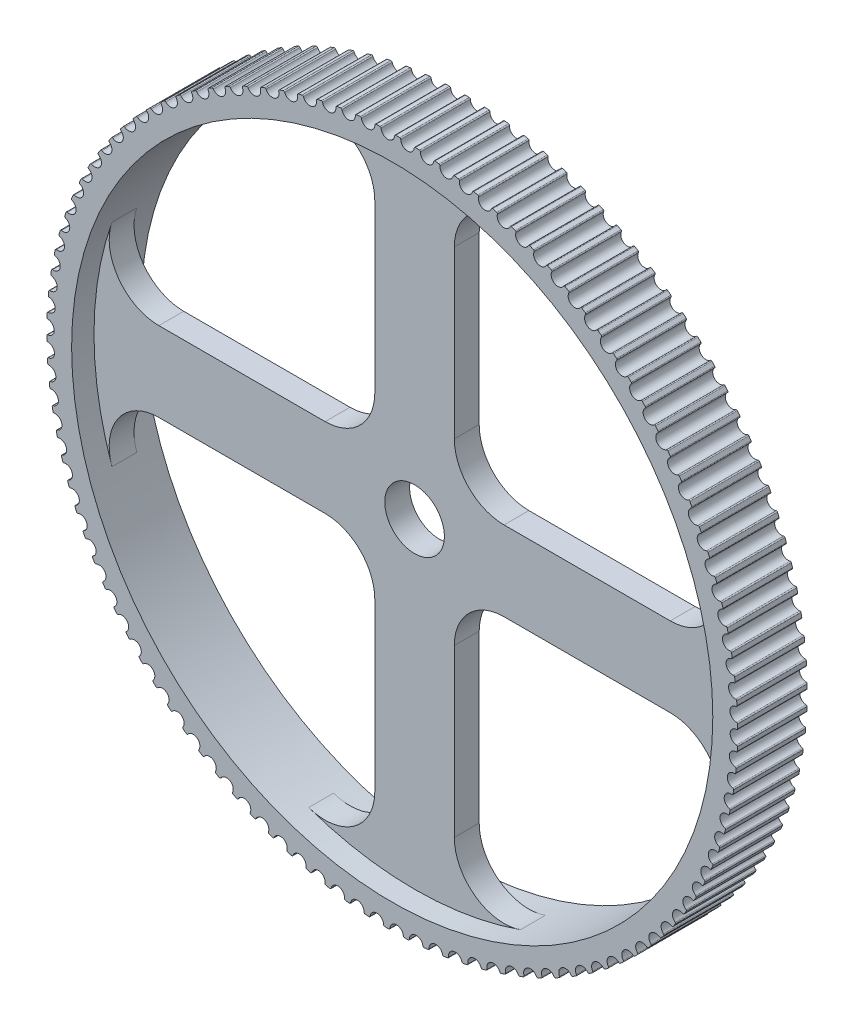
SolidWorks part; units mm, degrees
ref_plane "Front Plane" through (0, 0, 0) normal (0, 0, 1) x (1, 0, 0)
ref_plane "Top Plane" through (0, 0, 0) normal (0, 1, 0) x (1, 0, 0)
ref_plane "Right Plane" through (0, 0, 0) normal (1, 0, 0) x (0, 0, -1)
sketch "Sketch2" plane through (0, 0, 0) normal (0, 0, 1) x (1, 0, 0)
  circle A0 centre (0, 0) radius 35.03 construction
  arc A1 (-3.2113, 34.6013) -> (-3.0921, 34.5062) centre (-3.2012, 34.4918) cw
  arc A2 (-3.0921, 34.5062) -> (-1.738, 34.6009) centre (-2.418, 34.5956) ccw
  arc A3 (-1.738, 34.6009) -> (-1.6332, 34.7116) centre (-1.628, 34.6017) cw
  arc A4 (-1.6332, 34.7116) -> (-1.2307, 34.7282) centre (0, 0) cw
  circle A5 centre (0, 0) radius 34.75 construction
  circle A6 centre (0, 0) radius 34 construction
  arc A7 (0.3511, 34.7482) -> (0.7538, 34.7418) centre (0, 0) cw
  arc A8 (0.2401, 34.6437) -> (0.3511, 34.7482) centre (0.35, 34.6382) cw
  arc A9 (-1.1172, 34.6265) -> (0.2401, 34.6437) centre (-0.4391, 34.6772) ccw
  arc A10 (-1.2307, 34.7282) -> (-1.1172, 34.6265) centre (-1.2269, 34.6183) cw
  arc A11 (2.3343, 34.6715) -> (2.736, 34.6421) centre (0, 0) cw
  arc A12 (2.2175, 34.5735) -> (2.3343, 34.6715) centre (2.3269, 34.5618) cw
  arc A13 (0.8614, 34.6338) -> (2.2175, 34.5735) centre (1.5413, 34.6457) ccw
  arc A14 (0.7538, 34.7418) -> (0.8614, 34.6338) centre (0.7515, 34.6318) cw
  arc A15 (4.3098, 34.4817) -> (4.7092, 34.4294) centre (0, 0) cw
  arc A16 (4.1876, 34.3905) -> (4.3098, 34.4817) centre (4.2962, 34.3726) cw
  arc A17 (2.8372, 34.5281) -> (4.1876, 34.3905) centre (3.5167, 34.5012) ccw
  arc A18 (2.736, 34.6421) -> (2.8372, 34.5281) centre (2.7273, 34.5325) cw
  arc A19 (6.2713, 34.1794) -> (6.6671, 34.1044) centre (0, 0) cw
  arc A20 (6.1441, 34.0953) -> (6.2713, 34.1794) centre (6.2514, 34.0712) cw
  arc A21 (4.8038, 34.3098) -> (6.1441, 34.0953) centre (5.4806, 34.2442) ccw
  arc A22 (4.7092, 34.4294) -> (4.8038, 34.3098) centre (4.6943, 34.3204) cw
  arc A23 (8.2123, 33.7657) -> (8.6032, 33.6682) centre (0, 0) cw
  arc A24 (8.0806, 33.689) -> (8.2123, 33.7657) centre (8.1863, 33.6588) cw
  arc A25 (6.7547, 33.9796) -> (8.0806, 33.689) centre (7.4266, 33.8755) ccw
  arc A26 (6.6671, 34.1044) -> (6.7547, 33.9796) centre (6.646, 33.9965) cw
  arc A27 (10.1266, 33.2418) -> (10.5112, 33.1222) centre (0, 0) cw
  arc A28 (9.9906, 33.1727) -> (10.1266, 33.2418) centre (10.0945, 33.1365) cw
  arc A29 (8.6835, 33.5386) -> (9.9906, 33.1727) centre (9.3484, 33.3962) ccw
  arc A30 (8.6032, 33.6682) -> (8.6835, 33.5386) centre (8.5759, 33.5616) cw
  arc A31 (12.0078, 32.6094) -> (12.385, 32.4681) centre (0, 0) cw
  arc A32 (11.8681, 32.5482) -> (12.0078, 32.6094) centre (11.9698, 32.5062) cw
  arc A33 (10.584, 32.9882) -> (11.8681, 32.5482) centre (11.2397, 32.8081) ccw
  arc A34 (10.5112, 33.1222) -> (10.584, 32.9882) centre (10.4779, 33.0173) cw
  arc A35 (13.8498, 31.8707) -> (14.2183, 31.7081) centre (0, 0) cw
  arc A36 (13.7069, 31.8176) -> (13.8498, 31.8707) centre (13.806, 31.7699) cw
  arc A37 (12.45, 32.3301) -> (13.7069, 31.8176) centre (13.0944, 32.1129) ccw
  arc A38 (12.385, 32.4681) -> (12.45, 32.3301) centre (12.3458, 32.3653) cw
  arc A39 (15.6467, 31.0281) -> (16.0053, 30.8446) centre (0, 0) cw
  arc A40 (15.501, 30.9832) -> (15.6467, 31.0281) centre (15.5972, 30.9299) cw
  arc A41 (14.2754, 31.5667) -> (15.501, 30.9832) centre (14.9063, 31.313) ccw
  arc A42 (14.2183, 31.7081) -> (14.2754, 31.5667) centre (14.1733, 31.6077) cw
  arc A43 (17.3926, 30.0842) -> (17.7401, 29.8806) centre (0, 0) cw
  arc A44 (17.2445, 30.0478) -> (17.3926, 30.0842) centre (17.3375, 29.989) cw
  arc A45 (16.0542, 30.7002) -> (17.2445, 30.0478) centre (16.6696, 30.411) ccw
  arc A46 (16.0053, 30.8446) -> (16.0542, 30.7002) centre (15.9547, 30.747) cw
  arc A47 (19.0817, 29.0423) -> (19.417, 28.8191) centre (0, 0) cw
  arc A48 (18.9318, 29.0143) -> (19.0817, 29.0423) centre (19.0213, 28.9503) cw
  arc A49 (17.7807, 29.7336) -> (18.9318, 29.0143) centre (18.3786, 29.4097) ccw
  arc A50 (17.7401, 29.8806) -> (17.7807, 29.7336) centre (17.684, 29.786) cw
  arc A51 (20.7085, 27.9055) -> (21.0306, 27.6636) centre (0, 0) cw
  arc A52 (20.5573, 27.8862) -> (20.7085, 27.9055) centre (20.643, 27.8172) cw
  arc A53 (19.4491, 28.6701) -> (20.5573, 27.8862) centre (20.0276, 28.3125) ccw
  arc A54 (19.417, 28.8191) -> (19.4491, 28.6701) centre (19.3556, 28.7279) cw
  arc A55 (22.2679, 26.6778) -> (22.5756, 26.4179) centre (0, 0) cw
  arc A56 (22.1158, 26.6671) -> (22.2679, 26.6778) centre (22.1974, 26.5934) cw
  arc A57 (21.0542, 27.513) -> (22.1158, 26.6671) centre (21.6112, 27.123) ccw
  arc A58 (21.0306, 27.6636) -> (21.0542, 27.513) centre (20.964, 27.5761) cw
  arc A59 (23.7545, 25.363) -> (24.0469, 25.086) centre (0, 0) cw
  arc A60 (23.6021, 25.361) -> (23.7545, 25.363) centre (23.6793, 25.2828) cw
  arc A61 (22.5905, 26.2661) -> (23.6021, 25.361) centre (23.1244, 25.845) ccw
  arc A62 (22.5756, 26.4179) -> (22.5905, 26.2661) centre (22.5041, 26.3343) cw
  arc A63 (25.1637, 23.9656) -> (25.4399, 23.6723) centre (0, 0) cw
  arc A64 (25.0114, 23.9723) -> (25.1637, 23.9656) centre (25.0841, 23.8897) cw
  arc A65 (24.0532, 24.9336) -> (25.0114, 23.9723) centre (24.5621, 24.4827) ccw
  arc A66 (24.0469, 25.086) -> (24.0532, 24.9336) centre (23.9708, 25.0066) cw
  arc A67 (26.4909, 22.4899) -> (26.7498, 22.1813) centre (0, 0) cw
  arc A68 (26.3392, 22.5053) -> (26.4909, 22.4899) centre (26.407, 22.4187) cw
  arc A69 (25.4374, 23.5198) -> (26.3392, 22.5053) centre (25.9198, 23.0406) ccw
  arc A70 (25.4399, 23.6723) -> (25.4374, 23.5198) centre (25.3593, 23.5973) cw
  arc A71 (27.7316, 20.9409) -> (27.9725, 20.618) centre (0, 0) cw
  arc A72 (27.581, 20.9649) -> (27.7316, 20.9409) centre (27.6438, 20.8746) cw
  arc A73 (26.7386, 22.0293) -> (27.581, 20.9649) centre (27.1929, 21.5233) ccw
  arc A74 (26.7498, 22.1813) -> (26.7386, 22.0293) centre (26.6651, 22.1111) cw
  arc A75 (28.8819, 19.3236) -> (29.1039, 18.9875) centre (0, 0) cw
  arc A76 (28.7329, 19.3562) -> (28.8819, 19.3236) centre (28.7904, 19.2624) cw
  arc A77 (27.9526, 20.4669) -> (28.7329, 19.3562) centre (28.3772, 19.9358) ccw
  arc A78 (27.9725, 20.618) -> (27.9526, 20.4669) centre (27.8839, 20.5528) cw
  arc A79 (29.9379, 17.6432) -> (30.1404, 17.295) centre (0, 0) cw
  arc A80 (29.7911, 17.6843) -> (29.9379, 17.6432) centre (29.8431, 17.5874) cw
  arc A81 (29.0755, 18.8377) -> (29.7911, 17.6843) centre (29.4691, 18.2832) ccw
  arc A82 (29.1039, 18.9875) -> (29.0755, 18.8377) centre (29.0118, 18.9274) cw
  arc A83 (30.8963, 15.9053) -> (31.0786, 15.5461) centre (0, 0) cw
  arc A84 (30.752, 15.9547) -> (30.8963, 15.9053) centre (30.7985, 15.855) cw
  arc A85 (30.1035, 17.1471) -> (30.752, 15.9547) centre (30.4648, 16.571) ccw
  arc A86 (30.1404, 17.295) -> (30.1035, 17.1471) centre (30.045, 17.2403) cw
  arc A87 (31.7539, 14.1156) -> (31.9154, 13.7465) centre (0, 0) cw
  arc A88 (31.6127, 14.1731) -> (31.7539, 14.1156) centre (31.6534, 14.0709) cw
  arc A89 (31.0333, 15.4006) -> (31.6127, 14.1731) centre (31.3611, 14.8048) ccw
  arc A90 (31.0786, 15.5461) -> (31.0333, 15.4006) centre (30.9802, 15.4969) cw
  arc A91 (32.508, 12.2798) -> (32.6482, 11.9021) centre (0, 0) cw
  arc A92 (32.3703, 12.3452) -> (32.508, 12.2798) centre (32.4051, 12.2409) cw
  arc A93 (31.8619, 13.6038) -> (32.3703, 12.3452) centre (32.1552, 12.9903) ccw
  arc A94 (31.9154, 13.7465) -> (31.8619, 13.6038) centre (31.8144, 13.703) cw
  arc A95 (33.156, 10.4039) -> (33.2744, 10.0189) centre (0, 0) cw
  arc A96 (33.0223, 10.4771) -> (33.156, 10.4039) centre (33.0511, 10.371) cw
  arc A97 (32.5865, 11.7627) -> (33.0223, 10.4771) centre (32.8443, 11.1334) ccw
  arc A98 (32.6482, 11.9021) -> (32.5865, 11.7627) centre (32.5448, 11.8644) cw
  arc A99 (33.6959, 8.4941) -> (33.7921, 8.1029) centre (0, 0) cw
  arc A100 (33.5665, 8.5748) -> (33.6959, 8.4941) centre (33.5892, 8.4672) cw
  arc A101 (33.2049, 9.8831) -> (33.5665, 8.5748) centre (33.4263, 9.2402) ccw
  arc A102 (33.2744, 10.0189) -> (33.2049, 9.8831) centre (33.1691, 9.9871) cw
  arc A103 (34.1259, 6.5566) -> (34.1996, 6.1606) centre (0, 0) cw
  arc A104 (34.0013, 6.6446) -> (34.1259, 6.5566) centre (34.0178, 6.5358) cw
  arc A105 (33.7149, 7.9714) -> (34.0013, 6.6446) centre (33.8993, 7.3169) ccw
  arc A106 (33.7921, 8.1029) -> (33.7149, 7.9714) centre (33.6851, 8.0773) cw
  arc A107 (34.4445, 4.5977) -> (34.4955, 4.1981) centre (0, 0) cw
  arc A108 (34.3252, 4.6926) -> (34.4445, 4.5977) centre (34.3355, 4.5831) cw
  arc A109 (34.115, 6.0337) -> (34.3252, 4.6926) centre (34.2618, 5.3697) ccw
  arc A110 (34.1996, 6.1606) -> (34.115, 6.0337) centre (34.0913, 6.1411) cw
  arc A111 (34.6508, 2.6238) -> (34.6789, 2.2219) centre (0, 0) cw
  arc A112 (34.5371, 2.7254) -> (34.6508, 2.6238) centre (34.5411, 2.6155) cw
  arc A113 (34.4039, 4.0762) -> (34.5371, 2.7254) centre (34.5124, 3.4049) ccw
  arc A114 (34.4955, 4.1981) -> (34.4039, 4.0762) centre (34.3863, 4.1848) cw
  arc A115 (34.7441, 0.6413) -> (34.7492, 0.2385) centre (0, 0) cw
  arc A116 (34.6364, 0.7493) -> (34.7441, 0.6413) centre (34.6341, 0.6393) cw
  arc A117 (34.5805, 2.1055) -> (34.6364, 0.7493) centre (34.6505, 1.4291) ccw
  arc A118 (34.6789, 2.2219) -> (34.5805, 2.1055) centre (34.5691, 2.2149) cw
  arc A119 (34.724, -1.3432) -> (34.7061, -1.7456) centre (0, 0) cw
  arc A120 (34.6227, -1.2293) -> (34.724, -1.3432) centre (34.6141, -1.339) cw
  arc A121 (34.6443, 0.1279) -> (34.6227, -1.2293) centre (34.6756, -0.5514) ccw
  arc A122 (34.7492, 0.2385) -> (34.6443, 0.1279) centre (34.6392, 0.2378) cw
  arc A123 (34.5907, -3.3234) -> (34.5499, -3.7241) centre (0, 0) cw
  arc A124 (34.496, -3.2039) -> (34.5907, -3.3234) centre (34.4812, -3.3129) cw
  arc A125 (34.5951, -1.8501) -> (34.496, -3.2039) centre (34.5876, -2.5301) ccw
  arc A126 (34.7061, -1.7456) -> (34.5951, -1.8501) centre (34.5963, -1.7401) cw
  arc A127 (34.3446, -5.2927) -> (34.2809, -5.6905) centre (0, 0) cw
  arc A128 (34.2569, -5.168) -> (34.3446, -5.2927) centre (34.2359, -5.276) cw
  arc A129 (34.433, -3.8221) -> (34.2569, -5.168) centre (34.3867, -4.5005) ccw
  arc A130 (34.5499, -3.7241) -> (34.433, -3.8221) centre (34.4405, -3.7123) cw
  arc A131 (33.9864, -7.2448) -> (33.9001, -7.6382) centre (0, 0) cw
  arc A132 (33.906, -7.1152) -> (33.9864, -7.2448) centre (33.8788, -7.2218) cw
  arc A133 (34.1587, -5.7816) -> (33.906, -7.1152) centre (34.0737, -6.4563) ccw
  arc A134 (34.2809, -5.6905) -> (34.1587, -5.7816) centre (34.1724, -5.6724) cw
  arc A135 (33.5174, -9.1732) -> (33.4088, -9.5611) centre (0, 0) cw
  arc A136 (33.4445, -9.0393) -> (33.5174, -9.1732) centre (33.4113, -9.1442) cw
  arc A137 (33.7729, -7.7222) -> (33.4445, -9.0393) centre (33.6496, -8.391) ccw
  arc A138 (33.9001, -7.6382) -> (33.7729, -7.7222) centre (33.7928, -7.6141) cw
  arc A139 (32.939, -11.0717) -> (32.8085, -11.4528) centre (0, 0) cw
  arc A140 (32.8739, -10.9338) -> (32.939, -11.0717) centre (32.8348, -11.0367) cw
  arc A141 (33.277, -9.6377) -> (32.8739, -10.9338) centre (33.1157, -10.2983) ccw
  arc A142 (33.4088, -9.5611) -> (33.277, -9.6377) centre (33.303, -9.5308) cw
  arc A143 (32.2532, -12.9341) -> (32.1012, -13.3071) centre (0, 0) cw
  arc A144 (32.1961, -12.7927) -> (32.2532, -12.9341) centre (32.1511, -12.8932) cw
  arc A145 (32.6725, -11.5217) -> (32.1961, -12.7927) centre (32.4737, -12.172) ccw
  arc A146 (32.8085, -11.4528) -> (32.6725, -11.5217) centre (32.7046, -11.4165) cw
  arc A147 (31.4622, -14.7543) -> (31.2891, -15.118) centre (0, 0) cw
  arc A148 (31.4132, -14.6099) -> (31.4622, -14.7543) centre (31.3627, -14.7076) cw
  arc A149 (31.9614, -13.3682) -> (31.4132, -14.6099) centre (31.7259, -14.0061) ccw
  arc A150 (32.1012, -13.3071) -> (31.9614, -13.3682) centre (31.9995, -13.265) cw
  arc A151 (30.5686, -16.5264) -> (30.375, -16.8796) centre (0, 0) cw
  arc A152 (30.5279, -16.3794) -> (30.5686, -16.5264) centre (30.4719, -16.4741) cw
  arc A153 (31.1461, -15.171) -> (30.5279, -16.3794) centre (30.8746, -15.7944) ccw
  arc A154 (31.2891, -15.118) -> (31.1461, -15.171) centre (31.1901, -15.0701) cw
  arc A155 (29.5753, -18.2446) -> (29.3618, -18.5861) centre (0, 0) cw
  arc A156 (29.5431, -18.0955) -> (29.5753, -18.2446) centre (29.4817, -18.1868) cw
  arc A157 (30.2292, -16.9243) -> (29.5431, -18.0955) centre (29.9225, -17.5312) ccw
  arc A158 (30.375, -16.8796) -> (30.2292, -16.9243) centre (30.2789, -16.8262) cw
  arc A159 (28.4855, -19.9032) -> (28.2529, -20.2321) centre (0, 0) cw
  arc A160 (28.4618, -19.7526) -> (28.4855, -19.9032) centre (28.3953, -19.8402) cw
  arc A161 (29.2138, -18.6225) -> (28.4618, -19.7526) centre (28.8729, -19.2109) ccw
  arc A162 (29.3618, -18.5861) -> (29.2138, -18.6225) centre (29.2689, -18.5273) cw
  arc A163 (27.3028, -21.497) -> (27.0518, -21.812) centre (0, 0) cw
  arc A164 (27.2878, -21.3452) -> (27.3028, -21.497) centre (27.2164, -21.4289) cw
  arc A165 (28.103, -20.2599) -> (27.2878, -21.3452) centre (27.7291, -20.8279) ccw
  arc A166 (28.2529, -20.2321) -> (28.103, -20.2599) centre (28.1635, -20.168) cw
  arc A167 (26.031, -23.0206) -> (25.7625, -23.3208) centre (0, 0) cw
  arc A168 (26.0247, -22.8682) -> (26.031, -23.0206) centre (25.9486, -22.9477) cw
  arc A169 (26.9005, -21.8312) -> (26.0247, -22.8682) centre (26.4948, -22.3769) ccw
  arc A170 (27.0518, -21.812) -> (26.9005, -21.8312) centre (26.9662, -21.743) cw
  arc A171 (24.6744, -24.4691) -> (24.3891, -24.7535) centre (0, 0) cw
  arc A172 (24.6767, -24.3167) -> (24.6744, -24.4691) centre (24.5963, -24.3917) cw
  arc A173 (25.6103, -23.3313) -> (24.6767, -24.3167) centre (25.1741, -23.853) ccw
  arc A174 (25.7625, -23.3208) -> (25.6103, -23.3313) centre (25.6809, -23.247) cw
  arc A175 (23.2372, -25.8378) -> (22.9362, -26.1055) centre (0, 0) cw
  arc A176 (23.2483, -25.6858) -> (23.2372, -25.8378) centre (23.1637, -25.7561) cw
  arc A177 (24.2366, -24.7554) -> (23.2483, -25.6858) centre (23.7713, -25.2513) ccw
  arc A178 (24.3891, -24.7535) -> (24.2366, -24.7554) centre (24.3119, -24.6751) cw
  arc A179 (21.7243, -27.1223) -> (21.4084, -27.3723) centre (0, 0) cw
  arc A180 (21.744, -26.9711) -> (21.7243, -27.1223) centre (21.6555, -27.0364) cw
  arc A181 (22.7838, -26.0986) -> (21.744, -26.9711) centre (22.291, -26.5672) ccw
  arc A182 (22.9362, -26.1055) -> (22.7838, -26.0986) centre (22.8636, -26.0228) cw
  arc A183 (20.1405, -28.3183) -> (19.8109, -28.5498) centre (0, 0) cw
  arc A184 (20.1688, -28.1684) -> (20.1405, -28.3183) centre (20.0767, -28.2286) cw
  arc A185 (21.2567, -27.3568) -> (20.1688, -28.1684) centre (20.738, -27.7964) ccw
  arc A186 (21.4084, -27.3723) -> (21.2567, -27.3568) centre (21.3407, -27.2856) cw
  arc A187 (18.491, -29.4219) -> (18.1487, -29.6342) centre (0, 0) cw
  arc A188 (18.5278, -29.2739) -> (18.491, -29.4219) centre (18.4324, -29.3287) cw
  arc A189 (19.6603, -28.5257) -> (18.5278, -29.2739) centre (19.1173, -28.935) ccw
  arc A190 (19.8109, -28.5498) -> (19.6603, -28.5257) centre (19.7481, -28.4595) cw
  arc A191 (16.7811, -30.4295) -> (16.4273, -30.622) centre (0, 0) cw
  arc A192 (16.8263, -30.2839) -> (16.7811, -30.4295) centre (16.728, -30.3332) cw
  arc A193 (17.9997, -29.6015) -> (16.8263, -30.2839) centre (17.4342, -29.9792) ccw
  arc A194 (18.1487, -29.6342) -> (17.9997, -29.6015) centre (18.0912, -29.5404) cw
  arc A195 (15.0166, -31.3379) -> (14.6523, -31.5099) centre (0, 0) cw
  arc A196 (15.07, -31.1951) -> (15.0166, -31.3379) centre (14.969, -31.2387) cw
  arc A197 (16.2805, -30.5808) -> (15.07, -31.1951) centre (15.6943, -30.9256) ccw
  arc A198 (16.4273, -30.622) -> (16.2805, -30.5808) centre (16.3753, -30.5251) cw
  arc A199 (13.203, -32.1441) -> (12.8296, -32.295) centre (0, 0) cw
  arc A200 (13.2646, -32.0046) -> (13.203, -32.1441) centre (13.1613, -32.0423) cw
  arc A201 (14.5081, -31.4604) -> (13.2646, -32.0046) centre (13.9032, -31.7711) ccw
  arc A202 (14.6523, -31.5099) -> (14.5081, -31.4604) centre (14.6059, -31.4101) cw
  arc A203 (11.3464, -32.8454) -> (10.965, -32.9747) centre (0, 0) cw
  arc A204 (11.4158, -32.7096) -> (11.3464, -32.8454) centre (11.3105, -32.7414) cw
  arc A205 (12.6884, -32.2373) -> (11.4158, -32.7096) centre (12.0668, -32.513) ccw
  arc A206 (12.8296, -32.295) -> (12.6884, -32.2373) centre (12.789, -32.1927) cw
  arc A207 (9.4528, -33.4396) -> (9.0646, -33.5469) centre (0, 0) cw
  arc A208 (9.5299, -33.308) -> (9.4528, -33.4396) centre (9.4229, -33.3337) cw
  arc A209 (10.8273, -32.9091) -> (9.5299, -33.308) centre (10.191, -33.1489) ccw
  arc A210 (10.965, -32.9747) -> (10.8273, -32.9091) centre (10.9302, -32.8703) cw
  arc A211 (7.5284, -33.9247) -> (7.1347, -34.0097) centre (0, 0) cw
  arc A212 (7.6128, -33.7977) -> (7.5284, -33.9247) centre (7.5046, -33.8173) cw
  arc A213 (8.9309, -33.4736) -> (7.6128, -33.7977) centre (8.2819, -33.6766) ccw
  arc A214 (9.0646, -33.5469) -> (8.9309, -33.4736) centre (9.0359, -33.4407) cw
  arc A215 (5.5794, -34.2992) -> (5.1814, -34.3615) centre (0, 0) cw
  arc A216 (5.6709, -34.1772) -> (5.5794, -34.2992) centre (5.5617, -34.1906) cw
  arc A217 (7.0054, -33.9288) -> (5.6709, -34.1772) centre (6.3459, -34.0945) ccw
  arc A218 (7.1347, -34.0097) -> (7.0054, -33.9288) centre (7.1121, -33.902) cw
  arc A219 (3.6122, -34.5617) -> (3.2113, -34.6013) centre (0, 0) cw
  arc A220 (3.7105, -34.4452) -> (3.6122, -34.5617) centre (3.6008, -34.4523) cw
  arc A221 (5.057, -34.2734) -> (3.7105, -34.4452) centre (4.3891, -34.4011) ccw
  arc A222 (5.1814, -34.3615) -> (5.057, -34.2734) centre (5.165, -34.2528) cw
  arc A223 (1.6332, -34.7116) -> (1.2307, -34.7282) centre (0, 0) cw
  arc A224 (1.738, -34.6009) -> (1.6332, -34.7116) centre (1.628, -34.6017) cw
  arc A225 (3.0921, -34.5062) -> (1.738, -34.6009) centre (2.418, -34.5956) ccw
  arc A226 (3.2113, -34.6013) -> (3.0921, -34.5062) centre (3.2012, -34.4918) cw
  arc A227 (-0.3511, -34.7482) -> (-0.7538, -34.7418) centre (0, 0) cw
  arc A228 (-0.2401, -34.6437) -> (-0.3511, -34.7482) centre (-0.35, -34.6382) cw
  arc A229 (1.1172, -34.6265) -> (-0.2401, -34.6437) centre (0.4391, -34.6772) ccw
  arc A230 (1.2307, -34.7282) -> (1.1172, -34.6265) centre (1.2269, -34.6183) cw
  arc A231 (-2.3343, -34.6715) -> (-2.736, -34.6421) centre (0, 0) cw
  arc A232 (-2.2175, -34.5735) -> (-2.3343, -34.6715) centre (-2.3269, -34.5618) cw
  arc A233 (-0.8614, -34.6338) -> (-2.2175, -34.5735) centre (-1.5413, -34.6457) ccw
  arc A234 (-0.7538, -34.7418) -> (-0.8614, -34.6338) centre (-0.7515, -34.6318) cw
  arc A235 (-4.3098, -34.4817) -> (-4.7092, -34.4294) centre (0, 0) cw
  arc A236 (-4.1876, -34.3905) -> (-4.3098, -34.4817) centre (-4.2962, -34.3726) cw
  arc A237 (-2.8372, -34.5281) -> (-4.1876, -34.3905) centre (-3.5167, -34.5012) ccw
  arc A238 (-2.736, -34.6421) -> (-2.8372, -34.5281) centre (-2.7273, -34.5325) cw
  arc A239 (-6.2713, -34.1794) -> (-6.6671, -34.1044) centre (0, 0) cw
  arc A240 (-6.1441, -34.0953) -> (-6.2713, -34.1794) centre (-6.2514, -34.0712) cw
  arc A241 (-4.8038, -34.3098) -> (-6.1441, -34.0953) centre (-5.4806, -34.2442) ccw
  arc A242 (-4.7092, -34.4294) -> (-4.8038, -34.3098) centre (-4.6943, -34.3204) cw
  arc A243 (-8.2123, -33.7657) -> (-8.6032, -33.6682) centre (0, 0) cw
  arc A244 (-8.0806, -33.689) -> (-8.2123, -33.7657) centre (-8.1863, -33.6588) cw
  arc A245 (-6.7547, -33.9796) -> (-8.0806, -33.689) centre (-7.4266, -33.8755) ccw
  arc A246 (-6.6671, -34.1044) -> (-6.7547, -33.9796) centre (-6.646, -33.9965) cw
  arc A247 (-10.1266, -33.2418) -> (-10.5112, -33.1222) centre (0, 0) cw
  arc A248 (-9.9906, -33.1727) -> (-10.1266, -33.2418) centre (-10.0945, -33.1365) cw
  arc A249 (-8.6835, -33.5386) -> (-9.9906, -33.1727) centre (-9.3484, -33.3962) ccw
  arc A250 (-8.6032, -33.6682) -> (-8.6835, -33.5386) centre (-8.5759, -33.5616) cw
  arc A251 (-12.0078, -32.6094) -> (-12.385, -32.4681) centre (0, 0) cw
  arc A252 (-11.8681, -32.5482) -> (-12.0078, -32.6094) centre (-11.9698, -32.5062) cw
  arc A253 (-10.584, -32.9882) -> (-11.8681, -32.5482) centre (-11.2397, -32.8081) ccw
  arc A254 (-10.5112, -33.1222) -> (-10.584, -32.9882) centre (-10.4779, -33.0173) cw
  arc A255 (-13.8498, -31.8707) -> (-14.2183, -31.7081) centre (0, 0) cw
  arc A256 (-13.7069, -31.8176) -> (-13.8498, -31.8707) centre (-13.806, -31.7699) cw
  arc A257 (-12.45, -32.3301) -> (-13.7069, -31.8176) centre (-13.0944, -32.1129) ccw
  arc A258 (-12.385, -32.4681) -> (-12.45, -32.3301) centre (-12.3458, -32.3653) cw
  arc A259 (-15.6467, -31.0281) -> (-16.0053, -30.8446) centre (0, 0) cw
  arc A260 (-15.501, -30.9832) -> (-15.6467, -31.0281) centre (-15.5972, -30.9299) cw
  arc A261 (-14.2754, -31.5667) -> (-15.501, -30.9832) centre (-14.9063, -31.313) ccw
  arc A262 (-14.2183, -31.7081) -> (-14.2754, -31.5667) centre (-14.1733, -31.6077) cw
  arc A263 (-17.3926, -30.0842) -> (-17.7401, -29.8806) centre (0, 0) cw
  arc A264 (-17.2445, -30.0478) -> (-17.3926, -30.0842) centre (-17.3375, -29.989) cw
  arc A265 (-16.0542, -30.7002) -> (-17.2445, -30.0478) centre (-16.6696, -30.411) ccw
  arc A266 (-16.0053, -30.8446) -> (-16.0542, -30.7002) centre (-15.9547, -30.747) cw
  arc A267 (-19.0817, -29.0423) -> (-19.417, -28.8191) centre (0, 0) cw
  arc A268 (-18.9318, -29.0143) -> (-19.0817, -29.0423) centre (-19.0213, -28.9503) cw
  arc A269 (-17.7807, -29.7336) -> (-18.9318, -29.0143) centre (-18.3786, -29.4097) ccw
  arc A270 (-17.7401, -29.8806) -> (-17.7807, -29.7336) centre (-17.684, -29.786) cw
  arc A271 (-20.7085, -27.9055) -> (-21.0306, -27.6636) centre (0, 0) cw
  arc A272 (-20.5573, -27.8862) -> (-20.7085, -27.9055) centre (-20.643, -27.8172) cw
  arc A273 (-19.4491, -28.6701) -> (-20.5573, -27.8862) centre (-20.0276, -28.3125) ccw
  arc A274 (-19.417, -28.8191) -> (-19.4491, -28.6701) centre (-19.3556, -28.7279) cw
  arc A275 (-22.2679, -26.6778) -> (-22.5756, -26.4179) centre (0, 0) cw
  arc A276 (-22.1158, -26.6671) -> (-22.2679, -26.6778) centre (-22.1974, -26.5934) cw
  arc A277 (-21.0542, -27.513) -> (-22.1158, -26.6671) centre (-21.6112, -27.123) ccw
  arc A278 (-21.0306, -27.6636) -> (-21.0542, -27.513) centre (-20.964, -27.5761) cw
  arc A279 (-23.7545, -25.363) -> (-24.0469, -25.086) centre (0, 0) cw
  arc A280 (-23.6021, -25.361) -> (-23.7545, -25.363) centre (-23.6793, -25.2828) cw
  arc A281 (-22.5905, -26.2661) -> (-23.6021, -25.361) centre (-23.1244, -25.845) ccw
  arc A282 (-22.5756, -26.4179) -> (-22.5905, -26.2661) centre (-22.5041, -26.3343) cw
  arc A283 (-25.1637, -23.9656) -> (-25.4399, -23.6723) centre (0, 0) cw
  arc A284 (-25.0114, -23.9723) -> (-25.1637, -23.9656) centre (-25.0841, -23.8897) cw
  arc A285 (-24.0532, -24.9336) -> (-25.0114, -23.9723) centre (-24.5621, -24.4827) ccw
  arc A286 (-24.0469, -25.086) -> (-24.0532, -24.9336) centre (-23.9708, -25.0066) cw
  arc A287 (-26.4909, -22.4899) -> (-26.7498, -22.1813) centre (0, 0) cw
  arc A288 (-26.3392, -22.5053) -> (-26.4909, -22.4899) centre (-26.407, -22.4187) cw
  arc A289 (-25.4374, -23.5198) -> (-26.3392, -22.5053) centre (-25.9198, -23.0406) ccw
  arc A290 (-25.4399, -23.6723) -> (-25.4374, -23.5198) centre (-25.3593, -23.5973) cw
  arc A291 (-27.7316, -20.9409) -> (-27.9725, -20.618) centre (0, 0) cw
  arc A292 (-27.581, -20.9649) -> (-27.7316, -20.9409) centre (-27.6438, -20.8746) cw
  arc A293 (-26.7386, -22.0293) -> (-27.581, -20.9649) centre (-27.1929, -21.5233) ccw
  arc A294 (-26.7498, -22.1813) -> (-26.7386, -22.0293) centre (-26.6651, -22.1111) cw
  arc A295 (-28.8819, -19.3236) -> (-29.1039, -18.9875) centre (0, 0) cw
  arc A296 (-28.7329, -19.3562) -> (-28.8819, -19.3236) centre (-28.7904, -19.2624) cw
  arc A297 (-27.9526, -20.4669) -> (-28.7329, -19.3562) centre (-28.3772, -19.9358) ccw
  arc A298 (-27.9725, -20.618) -> (-27.9526, -20.4669) centre (-27.8839, -20.5528) cw
  arc A299 (-29.9379, -17.6432) -> (-30.1404, -17.295) centre (0, 0) cw
  arc A300 (-29.7911, -17.6843) -> (-29.9379, -17.6432) centre (-29.8431, -17.5874) cw
  arc A301 (-29.0755, -18.8377) -> (-29.7911, -17.6843) centre (-29.4691, -18.2832) ccw
  arc A302 (-29.1039, -18.9875) -> (-29.0755, -18.8377) centre (-29.0118, -18.9274) cw
  arc A303 (-30.8963, -15.9053) -> (-31.0786, -15.5461) centre (0, 0) cw
  arc A304 (-30.752, -15.9547) -> (-30.8963, -15.9053) centre (-30.7985, -15.855) cw
  arc A305 (-30.1035, -17.1471) -> (-30.752, -15.9547) centre (-30.4648, -16.571) ccw
  arc A306 (-30.1404, -17.295) -> (-30.1035, -17.1471) centre (-30.045, -17.2403) cw
  arc A307 (-31.7539, -14.1156) -> (-31.9154, -13.7465) centre (0, 0) cw
  arc A308 (-31.6127, -14.1731) -> (-31.7539, -14.1156) centre (-31.6534, -14.0709) cw
  arc A309 (-31.0333, -15.4006) -> (-31.6127, -14.1731) centre (-31.3611, -14.8048) ccw
  arc A310 (-31.0786, -15.5461) -> (-31.0333, -15.4006) centre (-30.9802, -15.4969) cw
  arc A311 (-32.508, -12.2798) -> (-32.6482, -11.9021) centre (0, 0) cw
  arc A312 (-32.3703, -12.3452) -> (-32.508, -12.2798) centre (-32.4051, -12.2409) cw
  arc A313 (-31.8619, -13.6038) -> (-32.3703, -12.3452) centre (-32.1552, -12.9903) ccw
  arc A314 (-31.9154, -13.7465) -> (-31.8619, -13.6038) centre (-31.8144, -13.703) cw
  arc A315 (-33.156, -10.4039) -> (-33.2744, -10.0189) centre (0, 0) cw
  arc A316 (-33.0223, -10.4771) -> (-33.156, -10.4039) centre (-33.0511, -10.371) cw
  arc A317 (-32.5865, -11.7627) -> (-33.0223, -10.4771) centre (-32.8443, -11.1334) ccw
  arc A318 (-32.6482, -11.9021) -> (-32.5865, -11.7627) centre (-32.5448, -11.8644) cw
  arc A319 (-33.6959, -8.4941) -> (-33.7921, -8.1029) centre (0, 0) cw
  arc A320 (-33.5665, -8.5748) -> (-33.6959, -8.4941) centre (-33.5892, -8.4672) cw
  arc A321 (-33.2049, -9.8831) -> (-33.5665, -8.5748) centre (-33.4263, -9.2402) ccw
  arc A322 (-33.2744, -10.0189) -> (-33.2049, -9.8831) centre (-33.1691, -9.9871) cw
  arc A323 (-34.1259, -6.5566) -> (-34.1996, -6.1606) centre (0, 0) cw
  arc A324 (-34.0013, -6.6446) -> (-34.1259, -6.5566) centre (-34.0178, -6.5358) cw
  arc A325 (-33.7149, -7.9714) -> (-34.0013, -6.6446) centre (-33.8993, -7.3169) ccw
  arc A326 (-33.7921, -8.1029) -> (-33.7149, -7.9714) centre (-33.6851, -8.0773) cw
  arc A327 (-34.4445, -4.5977) -> (-34.4955, -4.1981) centre (0, 0) cw
  arc A328 (-34.3252, -4.6926) -> (-34.4445, -4.5977) centre (-34.3355, -4.5831) cw
  arc A329 (-34.115, -6.0337) -> (-34.3252, -4.6926) centre (-34.2618, -5.3697) ccw
  arc A330 (-34.1996, -6.1606) -> (-34.115, -6.0337) centre (-34.0913, -6.1411) cw
  arc A331 (-34.6508, -2.6238) -> (-34.6789, -2.2219) centre (0, 0) cw
  arc A332 (-34.5371, -2.7254) -> (-34.6508, -2.6238) centre (-34.5411, -2.6155) cw
  arc A333 (-34.4039, -4.0762) -> (-34.5371, -2.7254) centre (-34.5124, -3.4049) ccw
  arc A334 (-34.4955, -4.1981) -> (-34.4039, -4.0762) centre (-34.3863, -4.1848) cw
  arc A335 (-34.7441, -0.6413) -> (-34.7492, -0.2385) centre (0, 0) cw
  arc A336 (-34.6364, -0.7493) -> (-34.7441, -0.6413) centre (-34.6341, -0.6393) cw
  arc A337 (-34.5805, -2.1055) -> (-34.6364, -0.7493) centre (-34.6505, -1.4291) ccw
  arc A338 (-34.6789, -2.2219) -> (-34.5805, -2.1055) centre (-34.5691, -2.2149) cw
  arc A339 (-34.724, 1.3432) -> (-34.7061, 1.7456) centre (0, 0) cw
  arc A340 (-34.6227, 1.2293) -> (-34.724, 1.3432) centre (-34.6141, 1.339) cw
  arc A341 (-34.6443, -0.1279) -> (-34.6227, 1.2293) centre (-34.6756, 0.5514) ccw
  arc A342 (-34.7492, -0.2385) -> (-34.6443, -0.1279) centre (-34.6392, -0.2378) cw
  arc A343 (-34.5907, 3.3234) -> (-34.5499, 3.7241) centre (0, 0) cw
  arc A344 (-34.496, 3.2039) -> (-34.5907, 3.3234) centre (-34.4812, 3.3129) cw
  arc A345 (-34.5951, 1.8501) -> (-34.496, 3.2039) centre (-34.5876, 2.5301) ccw
  arc A346 (-34.7061, 1.7456) -> (-34.5951, 1.8501) centre (-34.5963, 1.7401) cw
  arc A347 (-34.3446, 5.2927) -> (-34.2809, 5.6905) centre (0, 0) cw
  arc A348 (-34.2569, 5.168) -> (-34.3446, 5.2927) centre (-34.2359, 5.276) cw
  arc A349 (-34.433, 3.8221) -> (-34.2569, 5.168) centre (-34.3867, 4.5005) ccw
  arc A350 (-34.5499, 3.7241) -> (-34.433, 3.8221) centre (-34.4405, 3.7123) cw
  arc A351 (-33.9864, 7.2448) -> (-33.9001, 7.6382) centre (0, 0) cw
  arc A352 (-33.906, 7.1152) -> (-33.9864, 7.2448) centre (-33.8788, 7.2218) cw
  arc A353 (-34.1587, 5.7816) -> (-33.906, 7.1152) centre (-34.0737, 6.4563) ccw
  arc A354 (-34.2809, 5.6905) -> (-34.1587, 5.7816) centre (-34.1724, 5.6724) cw
  arc A355 (-33.5174, 9.1732) -> (-33.4088, 9.5611) centre (0, 0) cw
  arc A356 (-33.4445, 9.0393) -> (-33.5174, 9.1732) centre (-33.4113, 9.1442) cw
  arc A357 (-33.7729, 7.7222) -> (-33.4445, 9.0393) centre (-33.6496, 8.391) ccw
  arc A358 (-33.9001, 7.6382) -> (-33.7729, 7.7222) centre (-33.7928, 7.6141) cw
  arc A359 (-32.939, 11.0717) -> (-32.8085, 11.4528) centre (0, 0) cw
  arc A360 (-32.8739, 10.9338) -> (-32.939, 11.0717) centre (-32.8348, 11.0367) cw
  arc A361 (-33.277, 9.6377) -> (-32.8739, 10.9338) centre (-33.1157, 10.2983) ccw
  arc A362 (-33.4088, 9.5611) -> (-33.277, 9.6377) centre (-33.303, 9.5308) cw
  arc A363 (-32.2532, 12.9341) -> (-32.1012, 13.3071) centre (0, 0) cw
  arc A364 (-32.1961, 12.7927) -> (-32.2532, 12.9341) centre (-32.1511, 12.8932) cw
  arc A365 (-32.6725, 11.5217) -> (-32.1961, 12.7927) centre (-32.4737, 12.172) ccw
  arc A366 (-32.8085, 11.4528) -> (-32.6725, 11.5217) centre (-32.7046, 11.4165) cw
  arc A367 (-31.4622, 14.7543) -> (-31.2891, 15.118) centre (0, 0) cw
  arc A368 (-31.4132, 14.6099) -> (-31.4622, 14.7543) centre (-31.3627, 14.7076) cw
  arc A369 (-31.9614, 13.3682) -> (-31.4132, 14.6099) centre (-31.7259, 14.0061) ccw
  arc A370 (-32.1012, 13.3071) -> (-31.9614, 13.3682) centre (-31.9995, 13.265) cw
  arc A371 (-30.5686, 16.5264) -> (-30.375, 16.8796) centre (0, 0) cw
  arc A372 (-30.5279, 16.3794) -> (-30.5686, 16.5264) centre (-30.4719, 16.4741) cw
  arc A373 (-31.1461, 15.171) -> (-30.5279, 16.3794) centre (-30.8746, 15.7944) ccw
  arc A374 (-31.2891, 15.118) -> (-31.1461, 15.171) centre (-31.1901, 15.0701) cw
  arc A375 (-29.5753, 18.2446) -> (-29.3618, 18.5861) centre (0, 0) cw
  arc A376 (-29.5431, 18.0955) -> (-29.5753, 18.2446) centre (-29.4817, 18.1868) cw
  arc A377 (-30.2292, 16.9243) -> (-29.5431, 18.0955) centre (-29.9225, 17.5312) ccw
  arc A378 (-30.375, 16.8796) -> (-30.2292, 16.9243) centre (-30.2789, 16.8262) cw
  arc A379 (-28.4855, 19.9032) -> (-28.2529, 20.2321) centre (0, 0) cw
  arc A380 (-28.4618, 19.7526) -> (-28.4855, 19.9032) centre (-28.3953, 19.8402) cw
  arc A381 (-29.2138, 18.6225) -> (-28.4618, 19.7526) centre (-28.8729, 19.2109) ccw
  arc A382 (-29.3618, 18.5861) -> (-29.2138, 18.6225) centre (-29.2689, 18.5273) cw
  arc A383 (-27.3028, 21.497) -> (-27.0518, 21.812) centre (0, 0) cw
  arc A384 (-27.2878, 21.3452) -> (-27.3028, 21.497) centre (-27.2164, 21.4289) cw
  arc A385 (-28.103, 20.2599) -> (-27.2878, 21.3452) centre (-27.7291, 20.8279) ccw
  arc A386 (-28.2529, 20.2321) -> (-28.103, 20.2599) centre (-28.1635, 20.168) cw
  arc A387 (-26.031, 23.0206) -> (-25.7625, 23.3208) centre (0, 0) cw
  arc A388 (-26.0247, 22.8682) -> (-26.031, 23.0206) centre (-25.9486, 22.9477) cw
  arc A389 (-26.9005, 21.8312) -> (-26.0247, 22.8682) centre (-26.4948, 22.3769) ccw
  arc A390 (-27.0518, 21.812) -> (-26.9005, 21.8312) centre (-26.9662, 21.743) cw
  arc A391 (-24.6744, 24.4691) -> (-24.3891, 24.7535) centre (0, 0) cw
  arc A392 (-24.6767, 24.3167) -> (-24.6744, 24.4691) centre (-24.5963, 24.3917) cw
  arc A393 (-25.6103, 23.3313) -> (-24.6767, 24.3167) centre (-25.1741, 23.853) ccw
  arc A394 (-25.7625, 23.3208) -> (-25.6103, 23.3313) centre (-25.6809, 23.247) cw
  arc A395 (-23.2372, 25.8378) -> (-22.9362, 26.1055) centre (0, 0) cw
  arc A396 (-23.2483, 25.6858) -> (-23.2372, 25.8378) centre (-23.1637, 25.7561) cw
  arc A397 (-24.2366, 24.7554) -> (-23.2483, 25.6858) centre (-23.7713, 25.2513) ccw
  arc A398 (-24.3891, 24.7535) -> (-24.2366, 24.7554) centre (-24.3119, 24.6751) cw
  arc A399 (-21.7243, 27.1223) -> (-21.4084, 27.3723) centre (0, 0) cw
  arc A400 (-21.744, 26.9711) -> (-21.7243, 27.1223) centre (-21.6555, 27.0364) cw
  arc A401 (-22.7838, 26.0986) -> (-21.744, 26.9711) centre (-22.291, 26.5672) ccw
  arc A402 (-22.9362, 26.1055) -> (-22.7838, 26.0986) centre (-22.8636, 26.0228) cw
  arc A403 (-20.1405, 28.3183) -> (-19.8109, 28.5498) centre (0, 0) cw
  arc A404 (-20.1688, 28.1684) -> (-20.1405, 28.3183) centre (-20.0767, 28.2286) cw
  arc A405 (-21.2567, 27.3568) -> (-20.1688, 28.1684) centre (-20.738, 27.7964) ccw
  arc A406 (-21.4084, 27.3723) -> (-21.2567, 27.3568) centre (-21.3407, 27.2856) cw
  arc A407 (-18.491, 29.4219) -> (-18.1487, 29.6342) centre (0, 0) cw
  arc A408 (-18.5278, 29.2739) -> (-18.491, 29.4219) centre (-18.4324, 29.3287) cw
  arc A409 (-19.6603, 28.5257) -> (-18.5278, 29.2739) centre (-19.1173, 28.935) ccw
  arc A410 (-19.8109, 28.5498) -> (-19.6603, 28.5257) centre (-19.7481, 28.4595) cw
  arc A411 (-16.7811, 30.4295) -> (-16.4273, 30.622) centre (0, 0) cw
  arc A412 (-16.8263, 30.2839) -> (-16.7811, 30.4295) centre (-16.728, 30.3332) cw
  arc A413 (-17.9997, 29.6015) -> (-16.8263, 30.2839) centre (-17.4342, 29.9792) ccw
  arc A414 (-18.1487, 29.6342) -> (-17.9997, 29.6015) centre (-18.0912, 29.5404) cw
  arc A415 (-15.0166, 31.3379) -> (-14.6523, 31.5099) centre (0, 0) cw
  arc A416 (-15.07, 31.1951) -> (-15.0166, 31.3379) centre (-14.969, 31.2387) cw
  arc A417 (-16.2805, 30.5808) -> (-15.07, 31.1951) centre (-15.6943, 30.9256) ccw
  arc A418 (-16.4273, 30.622) -> (-16.2805, 30.5808) centre (-16.3753, 30.5251) cw
  arc A419 (-13.203, 32.1441) -> (-12.8296, 32.295) centre (0, 0) cw
  arc A420 (-13.2646, 32.0046) -> (-13.203, 32.1441) centre (-13.1613, 32.0423) cw
  arc A421 (-14.5081, 31.4604) -> (-13.2646, 32.0046) centre (-13.9032, 31.7711) ccw
  arc A422 (-14.6523, 31.5099) -> (-14.5081, 31.4604) centre (-14.6059, 31.4101) cw
  arc A423 (-11.3464, 32.8454) -> (-10.965, 32.9747) centre (0, 0) cw
  arc A424 (-11.4158, 32.7096) -> (-11.3464, 32.8454) centre (-11.3105, 32.7414) cw
  arc A425 (-12.6884, 32.2373) -> (-11.4158, 32.7096) centre (-12.0668, 32.513) ccw
  arc A426 (-12.8296, 32.295) -> (-12.6884, 32.2373) centre (-12.789, 32.1927) cw
  arc A427 (-9.4528, 33.4396) -> (-9.0646, 33.5469) centre (0, 0) cw
  arc A428 (-9.5299, 33.308) -> (-9.4528, 33.4396) centre (-9.4229, 33.3337) cw
  arc A429 (-10.8273, 32.9091) -> (-9.5299, 33.308) centre (-10.191, 33.1489) ccw
  arc A430 (-10.965, 32.9747) -> (-10.8273, 32.9091) centre (-10.9302, 32.8703) cw
  arc A431 (-7.5284, 33.9247) -> (-7.1347, 34.0097) centre (0, 0) cw
  arc A432 (-7.6128, 33.7977) -> (-7.5284, 33.9247) centre (-7.5046, 33.8173) cw
  arc A433 (-8.9309, 33.4736) -> (-7.6128, 33.7977) centre (-8.2819, 33.6766) ccw
  arc A434 (-9.0646, 33.5469) -> (-8.9309, 33.4736) centre (-9.0359, 33.4407) cw
  arc A435 (-5.5794, 34.2992) -> (-5.1814, 34.3615) centre (0, 0) cw
  arc A436 (-5.6709, 34.1772) -> (-5.5794, 34.2992) centre (-5.5617, 34.1906) cw
  arc A437 (-7.0054, 33.9288) -> (-5.6709, 34.1772) centre (-6.3459, 34.0945) ccw
  arc A438 (-7.1347, 34.0097) -> (-7.0054, 33.9288) centre (-7.1121, 33.902) cw
  arc A439 (-3.6122, 34.5617) -> (-3.2113, 34.6013) centre (0, 0) cw
  arc A440 (-3.7105, 34.4452) -> (-3.6122, 34.5617) centre (-3.6008, 34.4523) cw
  arc A441 (-5.057, 34.2734) -> (-3.7105, 34.4452) centre (-4.3891, 34.4011) ccw
  arc A442 (-5.1814, 34.3615) -> (-5.057, 34.2734) centre (-5.165, 34.2528) cw
  point P889 (0, 0)
  dimension "D1" = 70.06
  dimension "D2" = 0.11
  dimension "D3" = 0.68
  dimension "D4" = 69.5
  dimension "D5" = 68
  dimension "D6" = 110
extrude "Boss-Extrude1" add sketch "Sketch2" along normal mid plane 7
sketch "Sketch4" plane through (0, 0, 0) normal (0, 0, 1) x (1, 0, 0)
  circle A0 centre (0, 0) radius 32.25
  dimension "D1" = 64.5
extrude "Cut-Extrude2" cut sketch "Sketch4" against normal mid plane 7
sketch "Sketch5" plane through (0, 0, 3.5) normal (0, 0, 1) x (1, 0, 0)
  circle A0 centre (0, 0) radius 32.25
  circle A1 centre (0, 0) radius 36
  dimension "D1" = 72
sketch "Sketch6" plane through (0, 0, 0) normal (0, 0, 1) x (1, 0, 0)
  line L0 (0, 32.25) -> (0, -32.25) construction
  line L1 (-32.25, 0) -> (32.25, 0) construction
  line L2 (-4, 32.25) -> (-4, -32.25)
  line L3 (4, 32.25) -> (4, -32.25)
  line L4 (-32.25, -4) -> (32.25, -4)
  line L5 (-32.25, 4) -> (32.25, 4)
  line L6 (-4, 32.25) -> (4, 32.25)
  line L7 (32.25, 4) -> (32.25, -4)
  line L8 (-32.25, 4) -> (-32.25, -4)
  line L9 (-4, -32.25) -> (4, -32.25)
  circle A0 centre (0, 0) radius 32.25 construction
  circle A1 centre (0, 0) radius 3
  dimension "D3" = 6
  dimension "D1" = 4
  dimension "D2" = 4
extrude "Boss-Extrude2" add sketch "Sketch6" along normal mid plane 2.5 contours L6 L2 L5 L3 | L7 L5 L3 L4 | L5 L2 L4 L3 | L5 L8 L4 L2 | L2 L9 L3 L4
fillet "Fillet1" radius 5 4 edges at (-4, -4, 0) (4, -4, 0) (-4, 4, 0) (4, 4, 0)
fillet "Fillet2" radius 5 8 edges at (-4, -32.001, 0) (-4, 32.001, 0) (-32.001, -4, 0) (32.001, -4, 0) (-32.001, 4, 0) (32.001, 4, 0) (4, -32.001, 0) (4, 32.001, 0)
